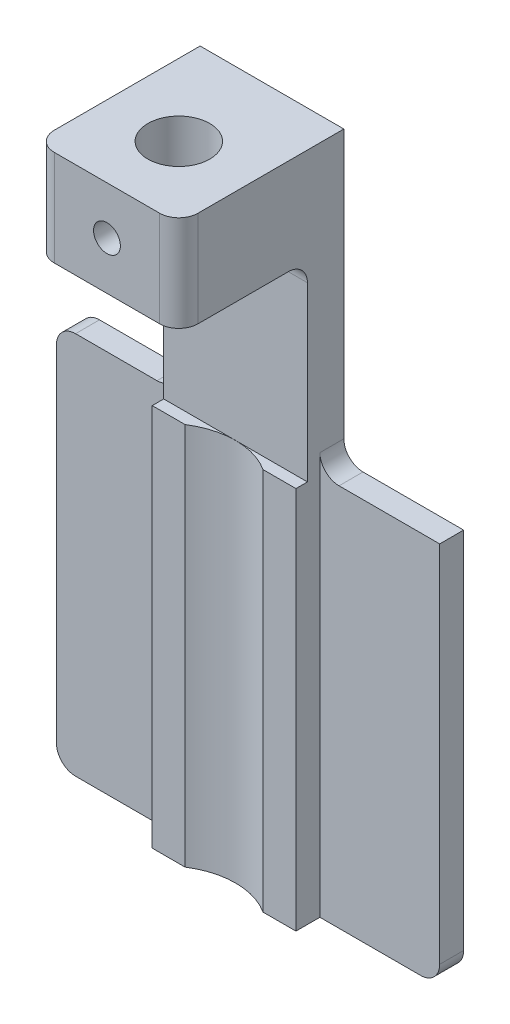
SolidWorks part; units mm, degrees
material "6061-T6 (SS)"
ref_plane "Front Plane" through (0, 0, 0) normal (0, 0, 1) x (1, 0, 0)
ref_plane "Top Plane" through (0, 0, 0) normal (0, 1, 0) x (1, 0, 0)
ref_plane "Right Plane" through (0, 0, 0) normal (1, 0, 0) x (0, 0, -1)
sketch "Sketch2" plane through (0, 0, 0) normal (1, 0, 0) x (0, 0, -1)
  line L0 (-4.7625, 12.7) -> (3, 12.7)
  line L1 (3, 12.7) -> (3, -25.4)
  line L2 (3, -25.4) -> (6.175, -25.4)
  line L3 (6.175, -25.4) -> (6.175, 19.05)
  line L4 (6.175, 19.05) -> (-4.7625, 19.05)
  line L5 (-4.7625, 19.05) -> (-4.7625, 12.7)
  line L6 (0, -1000) -> (0, 49000) construction
  dimension "D1" = 3
  dimension "D2" = 38.1
  dimension "D3" = 3.175
  dimension "D4" = 6.35
  dimension "D5" = 4.7625
  dimension "D6" = 12.7
extrude "Boss-Extrude1" add sketch "Sketch2" along normal mid plane 9.525
sketch "Sketch3" plane through (0, 19.05, 0) normal (0, 1, 0) x (1, 0, 0)
  circle A0 centre (0, 0) radius 2.05
  dimension "D1" = 4.1
extrude "Cut-Extrude1" cut sketch "Sketch3" against normal through all
sketch "Sketch4" plane through (0, -25.4, 0) normal (0, -1, 0) x (1, 0, 0)
  line L0 (4.7625, -3) -> (-4.7625, -3) construction
  circle A0 centre (0, 1.0005) radius 4.7625
  dimension "D1" = 9.525
  dimension "D2" = 0.762
extrude "Cut-Extrude2" cut sketch "Sketch4" against normal up to surface (38.1 mm away) up to face at (0, 12.7, 2.05)
sketch "Sketch5" plane through (0, 0, -6.175) normal (0, 0, -1) x (-1, 0, 0)
  line L1 (-12.7, 0) -> (12.7, 0)
  line L2 (-12.7, 0) -> (-12.7, -25.4)
  line L3 (-12.7, -25.4) -> (12.7, -25.4)
  line L4 (12.7, 0) -> (12.7, -25.4)
  line L5 (-12.7, 0) -> (12.7, -25.4) construction
  line L6 (-12.7, -25.4) -> (12.7, 0) construction
  line L7 (-4.7625, 12.7) -> (-2.5841, 12.7) construction
  point P0 (0, -12.7)
  dimension "D1" = 25.4
  dimension "D2" = 25.4
  dimension "D3" = 25.4
extrude "Boss-Extrude2" add sketch "Sketch5" against normal blind 1.5875
sketch "Sketch6" plane through (0, 0, -3) normal (0, 0, 1) x (1, 0, 0)
  line L0 (-2.5841, 12.7) -> (-4.7625, 12.7) construction
  line L1 (-8.7291, 12.7) -> (15.1624, 12.7)
  line L2 (-8.7291, 12.7) -> (-8.7291, 0)
  line L3 (-8.7291, 0) -> (15.1624, 0)
  line L4 (15.1624, 12.7) -> (15.1624, 0)
  dimension "D1" = 12.7
extrude "Cut-Extrude3" cut sketch "Sketch6" against normal blind 0.762
fillet "Fillet1" radius 1.27 8 edges at (-4.7625, 15.875, 4.7625) (4.7625, 15.875, 4.7625) (12.7, -25.4, -5.3813) (-12.7, -25.4, -5.3813) (-12.7, 0, -5.3813) (-4.7625, 0, -5.3813) (4.7625, 0, -5.3813) (0, 12.7, -3.762)
hole_wizard "#2-56 Tapped Hole1" positions "Sketch7" profile "Sketch8" tap size "#2-56" standard "ANSI Inch"
sketch "Sketch7" plane through (0, 0, 4.7625) normal (0, 0, 1) x (1, 0, 0)
  line L0 (3.4925, 19.05) -> (-3.4925, 19.05) construction
  point P0 (0, 15.875)
  dimension "D1" = 3.175
sketch "Sketch8" plane through (0, 15.875, 4.7625) normal (1, 0, 0) x (0, -1, 0)
  line L0 (0, 0) -> (0, 2.7125)
  line L1 (0, 2.7125) -> (0.889, 2.7125)
  line L2 (0.889, 2.7125) -> (0.889, 0)
  line L5 (0.889, 0) -> (0, 0)
  line L11 (0, -6.35) -> (0, 107.95) construction
  dimension "Thru Tap Drill Dia." = 1.778
  dimension "Thru Tap Drill Depth" = 2.7125
cosmetic thread "Hole Thread1" parameters "D2"=2.1844
